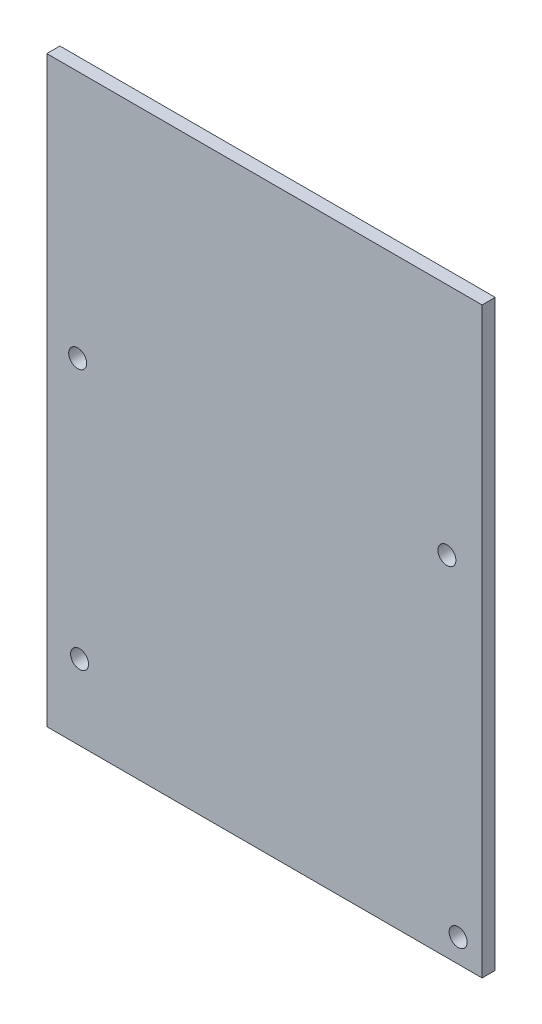
SolidWorks part; units mm, degrees
material "Rubber"
ref_plane "Front Plane" through (0, 0, 0) normal (0, 0, 1) x (1, 0, 0)
ref_plane "Top Plane" through (0, 0, 0) normal (0, 1, 0) x (1, 0, 0)
ref_plane "Right Plane" through (0, 0, 0) normal (1, 0, 0) x (0, 0, -1)
sketch "Sketch1" plane through (0, 0, 0) normal (0, 0, 1) x (1, 0, 0)
  line L1 (-29.5, 40.5) -> (29.5, 40.5)
  line L2 (-29.5, 40.5) -> (-29.5, -38.5)
  line L3 (-29.5, -38.5) -> (29.5, -38.5)
  line L4 (29.5, 40.5) -> (29.5, -38.5)
  dimension "D1" = 59
  dimension "D2" = 79
  dimension "D3" = 38.5
  dimension "D4" = 29.5
extrude "Extrude1" add sketch "Sketch1" along normal blind 1.778
hole_wizard "#2 Clearance Hole1" positions "3DSketch1" profile "Sketch2" hole size "#2" standard "Ansi Inch"
sketch3d "3DSketch1"
  line L0 (-29.5, -38.5, 1.778) -> (29.5, -38.5, 1.778) construction
  line L2 (-29.5, 40.5, 1.778) -> (-29.5, -38.5, 1.778) construction
  line L3 (29.5, -38.5, 0) -> (29.5, 40.5, 0) construction
  point P0 (-25.055, -28.34, 1.778)
  point P2 (-25.309, 6.839, 1.778)
  point P4 (24.729, 8.744, 1.778)
  point P6 (26.253, -35.325, 1.778)
  dimension "D1" = 10.16
  dimension "D2" = 4.445
  dimension "D9" = 3.7019
  dimension "D3" = 45.339
  dimension "D4" = 4.191
  dimension "D5" = 3.175
  dimension "D6" = 55.753
  dimension "D7" = 47.244
  dimension "D8" = 54.229
sketch "Sketch2" plane through (-25.055, -28.34, 1.778) normal (1, 0, 0) x (0, -1, 0)
  line L0 (0, 0) -> (0, 7.0826)
  line L1 (0, 7.0826) -> (1.2192, 6.35)
  line L2 (1.2192, 6.35) -> (1.2192, 0)
  line L5 (1.2192, 0) -> (0, 0)
  line L10 (0, 7.0826) -> (-1.2192, 6.35) construction
  line L11 (0, -6.35) -> (0, 107.95) construction
  dimension "Hole Dia." = 2.4384
  dimension "Hole Depth" = 6.35
  dimension "Drill Angle" = 118
